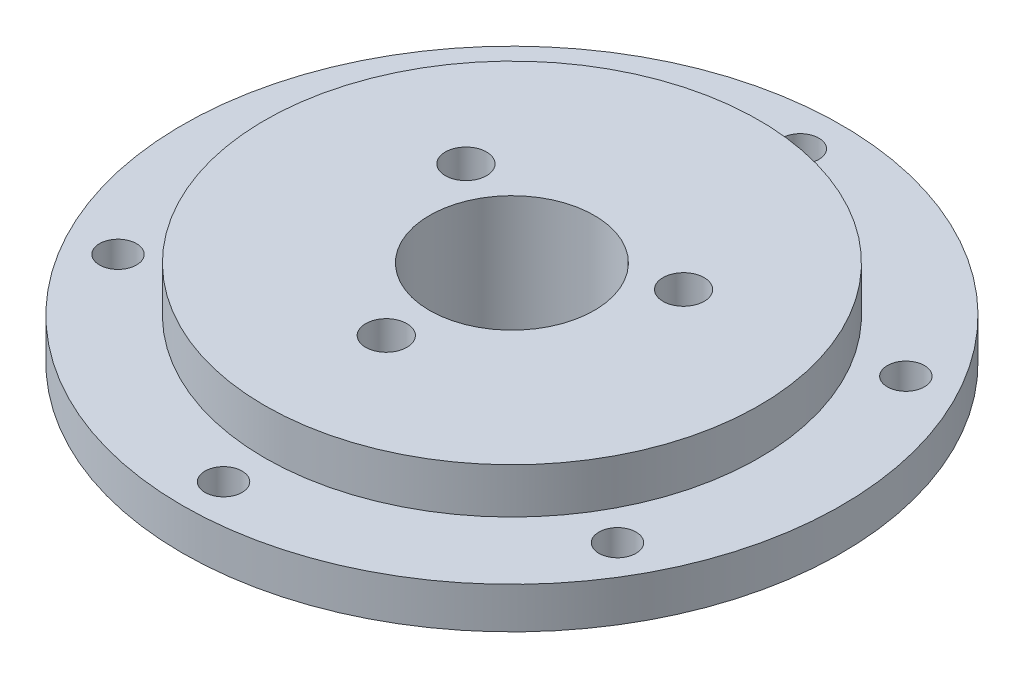
SolidWorks part; units mm, degrees
ref_plane "Front Plane" through (0, 0, 0) normal (0, 0, 1) x (1, 0, 0)
ref_plane "Top Plane" through (0, 0, 0) normal (0, 1, 0) x (1, 0, 0)
ref_plane "Right Plane" through (0, 0, 0) normal (1, 0, 0) x (0, 0, -1)
sketch "Sketch1" plane through (0, 0, 0) normal (0, 1, 0) x (1, 0, 0)
  circle A0 centre (0, 0) radius 40
  circle A1 centre (0, 0) radius 35 construction
  circle A2 centre (0, 35) radius 2.25
  circle A3 centre (0, 0) radius 35 construction
  circle A4 centre (30.3109, 17.5) radius 2.25
  circle A5 centre (0, 0) radius 35 construction
  circle A6 centre (30.3109, -17.5) radius 2.25
  circle A7 centre (0, 0) radius 35 construction
  circle A8 centre (0, -35) radius 2.25
  circle A9 centre (0, 0) radius 35 construction
  circle A10 centre (-30.3109, -17.5) radius 2.25
  circle A11 centre (0, 0) radius 35 construction
  circle A12 centre (-30.3109, 17.5) radius 2.25
  point P23 (0, 0)
  dimension "D1" = 80
  dimension "D2" = 70
  dimension "D3" = 4.5
  dimension "D4" = 6
extrude "Boss-Extrude1" add sketch "Sketch1" along normal blind 5
sketch "Sketch2" plane through (0, 5, 0) normal (0, 1, 0) x (1, 0, 0)
  circle A0 centre (0, 0) radius 30
  circle A1 centre (0, 0) radius 10
  circle A2 centre (0, 0) radius 15.25 construction
  circle A3 centre (0, -15.25) radius 2.5
  circle A4 centre (-13.2069, 7.625) radius 2.5
  circle A5 centre (13.2069, 7.625) radius 2.5
  point P14 (0, 0)
  dimension "D1" = 20
  dimension "D2" = 60
  dimension "D3" = 5
  dimension "D4" = 30.5
  dimension "D5" = 3
extrude "Boss-Extrude2" add sketch "Sketch2" along normal blind 5.5 and the other way offset from surface (10.5 mm away) 5.5 other way up to face at (0, 0, 40)
sketch "Sketch3" plane through (0, 10.5, 0) normal (0, 1, 0) x (1, 0, 0)
  circle A0 centre (0, -15.25) radius 2.5 construction
  circle A1 centre (13.2069, 7.625) radius 2.5 construction
  circle A3 centre (0, 0) radius 10 construction
  circle A4 centre (-13.2069, 7.625) radius 2.5 construction
  circle A5 centre (0, -15.25) radius 2.5
  circle A6 centre (13.2069, 7.625) radius 2.5
  circle A7 centre (0, 0) radius 10
  circle A8 centre (-13.2069, 7.625) radius 2.5
extrude "Cut-Extrude1" cut sketch "Sketch3" against normal through all
